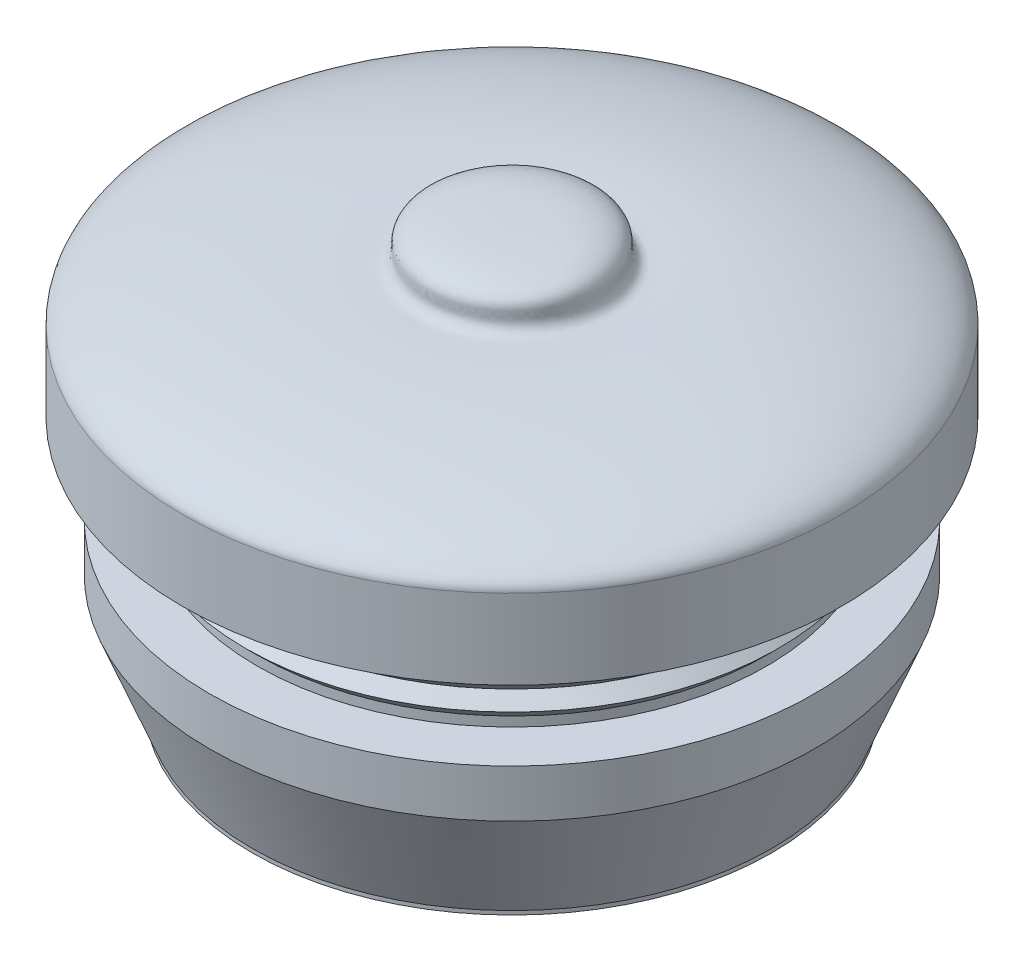
SolidWorks part; units mm, degrees
ref_plane "Front Plane" through (0, 0, 0) normal (0, 0, 1) x (1, 0, 0)
ref_plane "Top Plane" through (0, 0, 0) normal (0, 1, 0) x (1, 0, 0)
ref_plane "Right Plane" through (0, 0, 0) normal (1, 0, 0) x (0, 0, -1)
sketch "Sketch1" plane through (0, 0, 0) normal (1, 0, 0) x (0, 0, -1)
  line L0 (0, 6.8909) -> (0, -4.8654) construction
  line L1 (-10.35, -0.0831) -> (-10.35, 2.4169)
  line L2 (0.3942, 5.3169) -> (-0.3942, 5.3169) construction
  line L3 (-10.35, 3.6394) -> (-10.35, 2.1216) construction
  line L4 (-10.35, -0.0831) -> (-8, -0.0831)
  line L5 (-8, -0.0831) -> (-8, -0.3831)
  line L6 (-8, -0.3831) -> (-8.3667, -0.7498)
  line L7 (-8.3667, -0.7498) -> (-8, -1.1164)
  line L8 (-8, -1.1164) -> (-8.3667, -1.4831)
  line L9 (-8.3667, -1.4831) -> (-8, -1.8498)
  line L10 (-8, -1.8498) -> (-8.3667, -2.2164)
  line L11 (-8.3667, -2.2164) -> (-8, -2.5831)
  line L12 (-8, -2.5831) -> (-8, -2.8831)
  line L13 (-8, -2.8831) -> (-9.5, -2.8831)
  line L14 (-9.5, -2.8831) -> (-9.5, -4.3831)
  line L15 (-9.5, -4.3831) -> (-8.1595, -7.7621)
  line L16 (-8.1595, -7.7621) -> (-8.1595, -7.8831)
  line L17 (-8.1595, -7.8831) -> (-7.3058, -7.8831)
  line L18 (-7.3058, -7.8831) -> (-7.3058, -5.5331)
  line L19 (-7.3058, -5.5331) -> (-3.7597, -7.8831)
  line L20 (-3.7597, -7.8831) -> (-3.2879, -7.1712)
  line L21 (-3.2879, -7.1712) -> (-6.6834, -4.921)
  line L22 (-6.6834, -4.921) -> (-6.6834, 1.6481)
  line L23 (-6.6834, 1.6481) -> (-1.4009, 2.5658)
  line L24 (-1.4009, 2.5658) -> (-1.4009, 3.8821)
  line L25 (-1.4009, 3.8821) -> (0, 3.8821)
  line L26 (0, 3.8821) -> (0, 5.3169)
  line L27 (-8, -0.3831) -> (-8, -1.1164) construction
  spline S0 degree 3 poles (-10.35, 2.4169) (-10.35, 3.3655) (-5.8741, 4.2411) (-2.868, 4.0338) (-2.6116, 4.3242) (-2.7311, 4.7585) (-2.1974, 5.3602) (-0.4927, 5.3169) (0, 5.3169) knots 0 0 0 0 0.734908 0.759492 0.786959 0.823764 0.867169 1 1 1 1
  point P10 (-8, 1.4781)
  point P38 (-8.28, 1.5831)
  point P39 (-8.1595, -4.4653)
  point P40 (-8.1595, -6.1192)
  point P41 (-9.5, -2.7402)
  point P42 (0, 0)
  point P43 (-6.6834, -4.9277)
  point P44 (0, 0)
  dimension "D1" = 20.7
  dimension "D2" = 16
  dimension "D3" = 2.8
  dimension "D4" = 135
  dimension "D5" = 0.3
  dimension "D6" = 19
  dimension "D7" = 13.2
  dimension "D8" = 1.5
  dimension "D9" = 5
  dimension "D10" = 2.5
revolve "Revolve1" add sketch "Sketch1" angle 360 about L0
